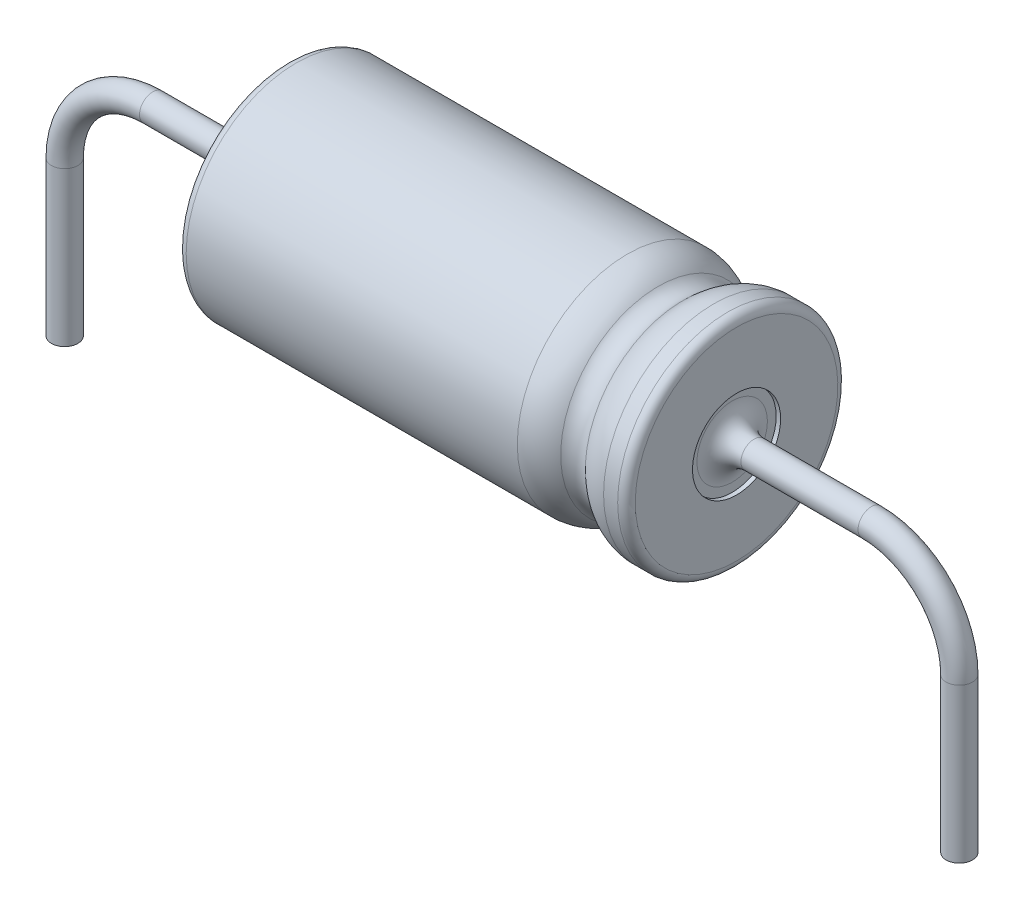
SolidWorks part; units mm, degrees
ref_plane "Front Plane" through (0, 0, 0) normal (0, 0, 1) x (1, 0, 0)
ref_plane "Top Plane" through (0, 0, 0) normal (0, 1, 0) x (1, 0, 0)
ref_plane "Right Plane" through (0, 0, 0) normal (1, 0, 0) x (0, 0, -1)
sketch "Sketch1" plane through (0, 0, 0) normal (0, 0, 1) x (1, 0, 0)
  line L1 (-10.16, 5) -> (-10.16, -3.3589) construction
  line L2 (-15.26, 5) -> (-5.06, 5)
  line L3 (-5.06, 2.5) -> (-29.8797, 2.5) construction
  line L4 (-5.06, 5) -> (-5.06, 2.5)
  line L5 (-15.26, 5) -> (-15.26, 2.5)
  dimension "D1" = 2.5
  dimension "D2" = 10.2
  dimension "D3" = 2.5
  dimension "D4" = 5.06
revolve "Base-Revolve-Thin" add sketch "Sketch1" angle 360 about L3
sketch "Sketch2" plane through (-5.06, 0, 0) normal (1, 0, 0) x (0, 0, -1)
  circle A0 centre (0, 2.5) radius 1
  dimension "D1" = 2
extrude "Cut-Extrude1" cut sketch "Sketch2" against normal blind 0.1
sketch "Sketch3" plane through (-15.26, 0, 0) normal (-1, 0, 0) x (0, 0, 1)
  circle A0 centre (0, 2.5) radius 1
  dimension "D1" = 2
extrude "Cut-Extrude2" cut sketch "Sketch3" against normal blind 0.1
fillet "Fillet1" radius 0.2 2 edges at (-15.26, 5, 0) (-5.06, 5, 0)
sketch "Sketch4" plane through (-5.16, 0, 0) normal (1, 0, 0) x (0, 0, -1)
  circle A0 centre (0, 2.5) radius 0.3
  dimension "D1" = 0.6
extrude "Boss-Extrude1" add sketch "Sketch4" along normal blind 0.62 and the other way blind 10.62
fillet "Fillet2" radius 0.5 2 edges at (-5.16, 2.5, -0.3) (-15.16, 2.2, 0)
sketch "Sketch5" plane through (0, 0, 0) normal (0, 0, 1) x (1, 0, 0)
  line L0 (0, 0.5) -> (0, -3)
  line L1 (-5.16, 2.5) -> (-5.06, 2.5) construction
  line L2 (-2, 2.5) -> (-4.54, 2.5)
  line L4 (0, 0.5) -> (-3.248, 0.5) construction
  line L5 (-10.16, 0) -> (-10.16, -2.8359) construction
  line L6 (-15.06, 0) -> (-5.26, 0) construction
  arc A0 (-2, 2.5) -> (0, 0.5) centre (-2, 0.5) cw
  dimension "D1" = 0.5
  dimension "D2" = 3
sketch "Sketch7" plane through (-4.54, 0, 0) normal (1, 0, 0) x (0, 0, -1)
  circle A1 centre (0, 2.5) radius 0.3
  circle A2 centre (0, 2.5) radius 0.3
  dimension "D1" = 0
sweep "Boss-Sweep2" add profiles "Sketch7" path "Sketch5"
ref_plane "Plane4" through (-10.16, 0, 0) normal (1, 0, 0) x (0, 0, -1)
mirror "Mirror1" about plane through (-10.16, 0, 0) normal (1, 0, 0) of "Boss-Sweep2"
sketch "Sketch8" plane through (0, 0, 0) normal (0, 0, 1) x (1, 0, 0)
  line L0 (-5.26, 5) -> (-15.06, 5) construction
  line L1 (-2.9791, 2.5) -> (-7.5151, 2.5) construction
  line L2 (-5.16, 2.5) -> (-5.06, 2.5) construction
  line L3 (-6.56, 5) -> (-6.56, 3.2058) construction
  line L4 (-5.06, 0.2) -> (-5.06, 4.8) construction
  line L5 (-5.5802, 5) -> (-7.5398, 5)
  arc A0 (-6.84, 4.7143) -> (-6.2801, 4.7143) centre (-6.56, 5) ccw
  arc A1 (-6.2801, 4.7143) -> (-5.5802, 5) centre (-5.5802, 4) cw
  arc A2 (-6.84, 4.7143) -> (-7.5398, 5) centre (-7.5398, 4) ccw
  dimension "D1" = 0.4
  dimension "D2" = 1
  dimension "D3" = 1.2201
  dimension "D4" = 0.2857
revolve "Cut-Revolve1" cut sketch "Sketch8" angle 360 about L1
ref_plane "Board Plane" through (0, -0.3, 0) normal (0, 1, 0) x (-1, 0, 0)
sketch "Component_Outline" plane through (0, -0.3, 0) normal (0, 1, 0) x (-1, 0, 0)
  line L0 (15.26, -2.3) -> (15.26, 2.3) construction
  line L1 (15.26, 2.5) -> (5.06, 2.5)
  line L2 (15.26, 2.5) -> (15.26, 0.5)
  line L3 (15.26, -2.5) -> (5.06, -2.5)
  line L4 (5.06, 2.5) -> (5.06, 0.5)
  line L5 (15.06, 2.5) -> (7.5398, 2.5) construction
  line L6 (5.06, 2.3) -> (5.06, -2.3) construction
  line L7 (7.5398, -2.5) -> (15.06, -2.5) construction
  line L8 (4.66, 0.3) -> (5.06, 0.5)
  line L9 (5.06, -0.5) -> (4.66, -0.3)
  line L10 (4.66, -0.3) -> (0, -0.3)
  line L11 (0, 0.3) -> (4.66, 0.3)
  line L12 (5.06, 1) -> (5.06, -1) construction
  line L13 (5.06, -0.5) -> (5.06, -2.5)
  line L14 (15.66, 0.3) -> (15.26, 0.5)
  line L15 (15.66, -0.3) -> (15.26, -0.5)
  line L16 (15.66, 0.3) -> (20.32, 0.3)
  line L17 (20.32, -0.3) -> (15.66, -0.3)
  line L18 (15.26, -0.5) -> (15.26, -2.5)
  arc A0 (4.66, 0.3) -> (5.16, 0.8) centre (4.66, 0.8) ccw construction
  arc A1 (0, -0.3) -> (0, 0.3) centre (0, 0) cw
  arc A2 (15.16, 0.8) -> (15.66, 0.3) centre (15.66, 0.8) ccw construction
  arc A3 (15.66, -0.3) -> (15.16, -0.8) centre (15.66, -0.8) ccw construction
  arc A4 (20.32, 0.3) -> (20.32, -0.3) centre (20.32, 0) cw
  circle A5 centre (20.32, 0) radius 0.3 construction
